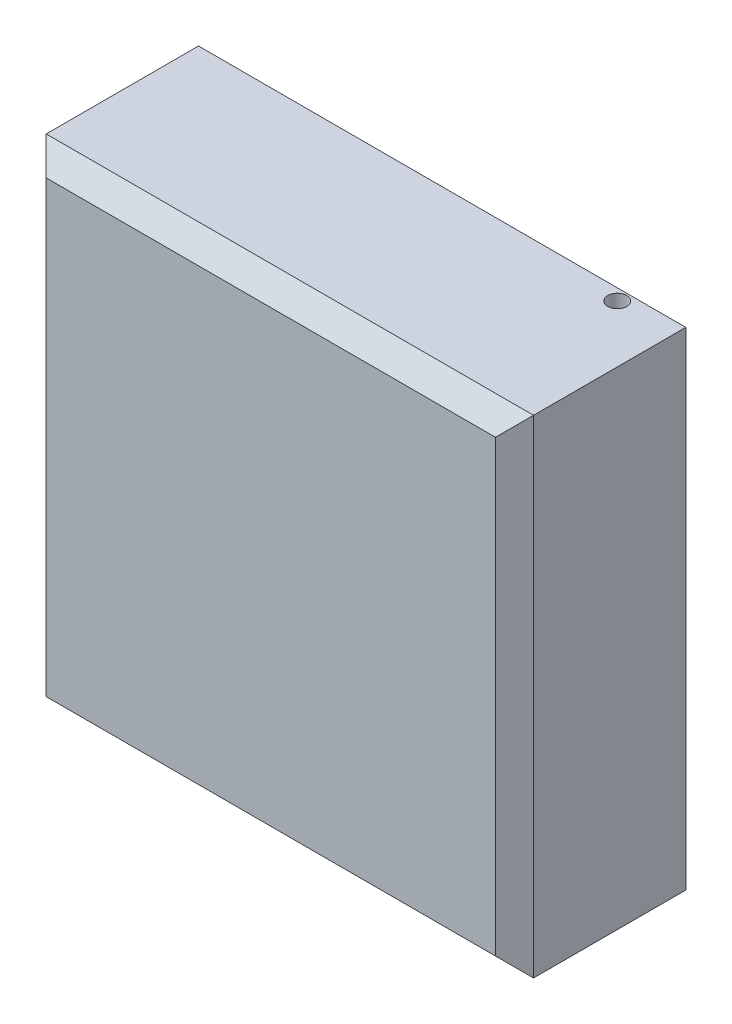
SolidWorks part; units mm, degrees
ref_plane "前基準面" through (0, 0, 0) normal (0, 0, 1) x (1, 0, 0)
ref_plane "上基準面" through (0, 0, 0) normal (0, 1, 0) x (1, 0, 0)
ref_plane "右基準面" through (0, 0, 0) normal (1, 0, 0) x (0, 0, -1)
sketch "草圖1" plane through (0, 0, 0) normal (0, 0, 1) x (1, 0, 0)
  line L1 (-128, 128) -> (128, 128)
  line L2 (-128, 128) -> (-128, -128)
  line L3 (-128, -128) -> (128, -128)
  line L4 (128, 128) -> (128, -128)
  line L5 (-128, 128) -> (128, -128) construction
  line L6 (-128, -128) -> (128, 128) construction
  point P0 (0, 0)
  dimension "D1" = 256
  dimension "D2" = 256
extrude "填料-伸長1" add sketch "草圖1" along normal blind 100
sketch "草圖2" plane through (0, -128, 0) normal (0, -1, 0) x (1, 0, 0)
  line L1 (-128, 0) -> (128, 0) construction
  line L2 (128, 100) -> (128, 0) construction
  circle A0 centre (98, 16) radius 5
  point P2 (0, 0)
  dimension "D2" = 10
  dimension "D1" = 30
  dimension "D3" = 16
extrude "除料-伸長1" cut sketch "草圖2" against normal through all
chamfer "導角1" distance 10 angle 45 8 edges at (0, 128, 0) (128, 0, 0) (-128, 0, 0) (0, -128, 0) (128, 0, 100) (0, 128, 100) (-128, 0, 100) (0, -128, 100)
